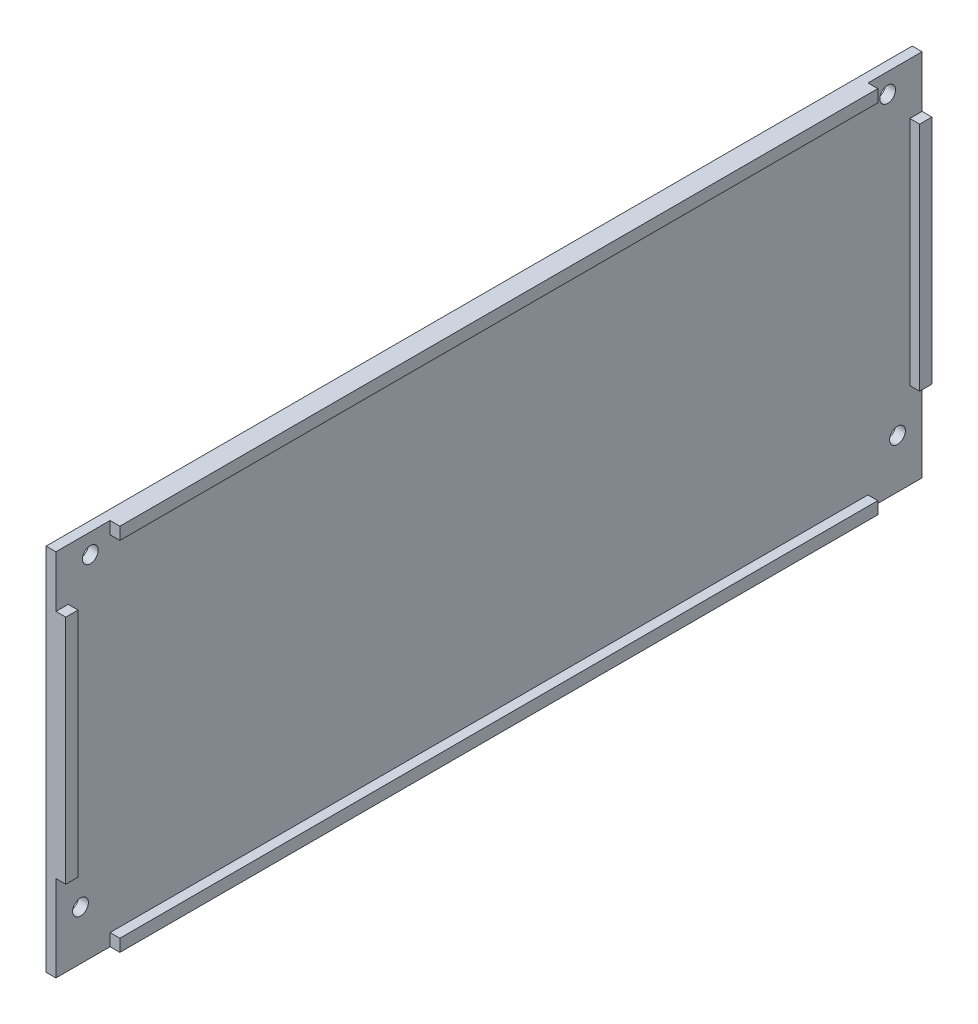
SolidWorks part; units mm, degrees
ref_plane "Front Plane" through (0, 0, 0) normal (0, 0, 1) x (1, 0, 0)
ref_plane "Top Plane" through (0, 0, 0) normal (0, 1, 0) x (1, 0, 0)
ref_plane "Right Plane" through (0, 0, 0) normal (1, 0, 0) x (0, 0, -1)
sketch "Sketch1" plane through (0, 0, 0) normal (1, 0, 0) x (0, 0, -1)
  line L0 (0, 0) -> (0, 64.2564) construction
  line L1 (-88, 37.5) -> (88, 37.5)
  line L2 (-88, 37.5) -> (-88, -37.5)
  line L3 (-88, -37.5) -> (88, -37.5)
  line L4 (88, 37.5) -> (88, -37.5)
  line L5 (-88, 37.5) -> (88, -37.5) construction
  line L6 (-88, -37.5) -> (88, 37.5) construction
  circle A0 centre (-81, 33.5) radius 1.6
  circle A1 centre (81, 33.5) radius 1.6
  circle A2 centre (-83, -27.5) radius 1.6
  circle A3 centre (83, -27.5) radius 1.6
  point P0 (0, 0)
  dimension "D3" = 7
  dimension "D5" = 5
  dimension "D1" = 176
  dimension "D2" = 75
  dimension "D4" = 4
  dimension "D6" = 10
extrude "Boss-Extrude1" add sketch "Sketch1" along normal blind 2
sketch "Sketch3" plane through (2, 0, 0) normal (1, 0, 0) x (0, 0, -1)
  line L0 (0, 0) -> (0, -67.6738) construction
  line L1 (-88, -37.5) -> (88, -37.5) construction
  line L2 (0, 0) -> (95.959, 0) construction
  line L3 (-77, -37.5) -> (77, -37.5)
  line L4 (-77, -37.5) -> (-77, -35)
  line L5 (-77, -35) -> (77, -35)
  line L6 (77, -37.5) -> (77, -35)
  line L7 (-77, 35) -> (77, 35)
  line L8 (77, 37.5) -> (77, 35)
  line L9 (-77, 37.5) -> (77, 37.5)
  line L10 (-77, 37.5) -> (-77, 35)
  point P9 (-77, -36.25)
  dimension "D1" = 2.5
  dimension "D2" = 77
  dimension "D3" = 77
extrude "Boss-Extrude2" add sketch "Sketch3" along normal blind 2
sketch "Sketch4" plane through (2, 0, 0) normal (1, 0, 0) x (0, 0, -1)
  line L0 (-88, 37.5) -> (-88, -37.5) construction
  line L1 (-88, 27) -> (-85.5, 27)
  line L2 (-88, 27) -> (-88, -20)
  line L3 (-88, -20) -> (-85.5, -20)
  line L4 (-85.5, 27) -> (-85.5, -20)
  line L5 (0, 0) -> (-103.8414, 0) construction
  line L6 (0, 0) -> (0, 44.2972) construction
  line L9 (88, -20) -> (85.5, -20)
  line L10 (85.5, 27) -> (85.5, -20)
  line L11 (88, 27) -> (85.5, 27)
  line L12 (88, 27) -> (88, -20)
  dimension "D1" = 2.5
  dimension "D2" = 27
  dimension "D3" = 20
extrude "Boss-Extrude3" add sketch "Sketch4" along normal blind 2
